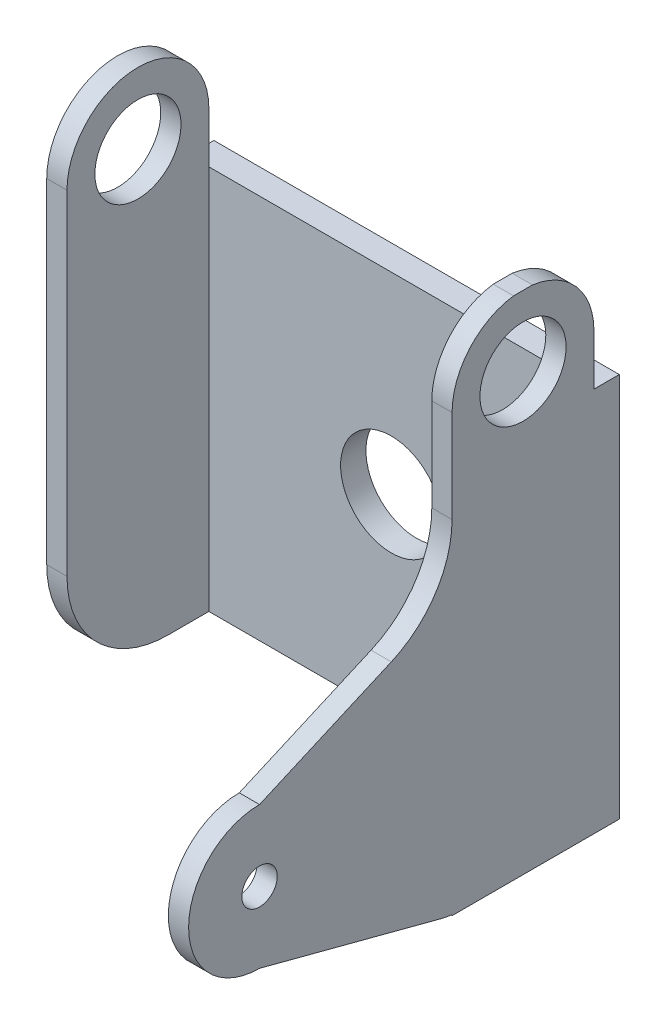
SolidWorks part; units mm, degrees
ref_plane "前视基准面" through (0, 0, 0) normal (0, 0, 1) x (1, 0, 0)
ref_plane "上视基准面" through (0, 0, 0) normal (0, 1, 0) x (1, 0, 0)
ref_plane "右视基准面" through (0, 0, 0) normal (1, 0, 0) x (0, 0, -1)
sketch "草图1" plane through (0, 0, 0) normal (0, 0, 1) x (1, 0, 0)
  line L1 (-20, -19) -> (20, -19)
  line L2 (-20, -19) -> (-20, 19)
  line L3 (-20, 19) -> (20, 19)
  line L4 (20, -19) -> (20, 19)
  line L5 (-20, -19) -> (20, 19) construction
  line L6 (-20, 19) -> (20, -19) construction
  circle A0 centre (0, 0) radius 5
  point P0 (0, 0)
  dimension "D3" = 10
  dimension "D1" = 40
  dimension "D2" = 38
extrude "凸台-拉伸1" add sketch "草图1" along normal blind 2.5
sketch "草图2" plane through (0, 0, 2.5) normal (0, 0, 1) x (1, 0, 0)
  line L0 (-18, 19) -> (-18, -19)
  line L4 (20, -19) -> (20, 19)
  line L5 (20, 19) -> (-20, 19)
  line L6 (-20, 19) -> (-20, -19)
  line L7 (-20, -19) -> (20, -19)
  line L10 (-20, 19) -> (-20, -19)
  line L12 (-18, 19) -> (-18, 31)
  line L13 (-18, 31) -> (-20, 31)
  line L14 (-20, 31) -> (-20, 19)
  line L15 (-20, -19) -> (-18, -19)
  line L16 (0, 28.2188) -> (0, -23.9099) construction
  line L20 (15.5, -19) -> (20, -19)
  line L21 (-20, -19) -> (20, -19) construction
  dimension "D2" = 2
  dimension "D4" = 38
  dimension "D5" = 12
  dimension "D1" = 0
extrude "凸台-拉伸2" add sketch "草图2" along normal blind 14 contours L0 L15 L10 L14 L13 L12
sketch "草图3" plane through (-18, 0, 0) normal (1, 0, 0) x (0, 0, -1)
  line L0 (-16.5, -19) -> (-16.5, 31) construction
  line L1 (-16.5, 31) -> (-2.5, 31) construction
  line L2 (-16.5, -19) -> (-2.5, -19) construction
  line L3 (-2.5, 19) -> (-2.5, -19) construction
  line L4 (-2.5, 31) -> (-2.5, 19) construction
  line L5 (-6.5, -19) -> (-2.5, -19)
  line L6 (-2.5, 19) -> (-2.5, -19)
  line L7 (-16.5, -9) -> (-16.5, 24)
  line L8 (-2.5, 24) -> (-2.5, 19)
  line L9 (-16.5, 24) -> (-16.5, -9)
  line L10 (-2.5, 24) -> (-2.5, -19)
  line L11 (-16.5, -19) -> (-16.5, 31)
  line L12 (-16.5, -19) -> (-2.5, -19)
  line L13 (-16.5, 24) -> (-16.5, 31)
  line L14 (-16.5, 31) -> (-2.5, 31) construction
  line L15 (-16.5, 31) -> (-2.5, 31)
  line L16 (-2.5, 31) -> (-2.5, 24)
  arc A0 (-2.5, 24) -> (-16.5, 24) centre (-9.5, 24) ccw
  arc A1 (-6.5, -19) -> (-16.5, -9) centre (-6.5, -9) cw
  circle A2 centre (-9.5, 24) radius 4.25
  line M1 (-2.5, 19) -> (-2.5, 31)
  line M2 (-2.5, 31) -> (-16.5, 31)
  line M3 (-16.5, 31) -> (-16.5, -19)
  line M4 (-16.5, -19) -> (-2.5, -19)
  dimension "D1" = 14
  dimension "D3" = 7
  dimension "D4" = 10
  dimension "D5" = 8.5
  dimension "D2" = 7
extrude "切除-拉伸2" cut sketch "草图3" against normal through all contours A1 M4 M3 | A0 L15 M3 | A0 M1 M2 | A2
sketch "草图4" plane through (0, 0, 2.5) normal (0, 0, 1) x (1, 0, 0)
  line L1 (20, 19) -> (-18, 19) construction
  line L2 (-18, -19) -> (20, -19) construction
  line L4 (18, -19) -> (18, 30.9375)
  line L5 (15.5, -19) -> (20, -19)
  line L6 (18, 30.9375) -> (20, 30.9375)
  line L7 (20, 30.9375) -> (20, 19)
  line L8 (20, 19) -> (-18, 19)
  line L9 (-18, 19) -> (-18, -19)
  line L10 (-18, -19) -> (20, -19)
  line L11 (20, -19) -> (20, 19)
  line L12 (20, 19) -> (15.5, 19)
  line L14 (15.5, -19) -> (20, -19)
  line L15 (20, -19) -> (20, 19)
  line M7 (20, 19) -> (-18, 19)
  line M9 (-18, -19) -> (20, -19)
  line M10 (20, -19) -> (20, 19)
  dimension "D1" = 2
  dimension "D3" = 50
  dimension "D2" = 0
extrude "凸台-拉伸3" add sketch "草图4" along normal blind 40 contours L7 L6 L4 M7 | L4 M9 M10 M7
sketch "草图5" plane through (20, 0, 0) normal (1, 0, 0) x (0, 0, -1)
  line L0 (-2.5, 25) -> (-2.5, -19)
  line L1 (-16.5, 24) -> (-16.5, 14.8521)
  line L2 (-6.5, -19) -> (-2.5, -19)
  line L3 (-16.5, -18.916) -> (-16.5, -19)
  line L4 (-15.2062, -19) -> (-13.4997, -19)
  line L5 (-35.5, -14) -> (-17.7512, -18.6707)
  line L6 (0, -19) -> (0, 19)
  line L7 (0, 19) -> (-2.5, 19)
  line L8 (-2.5, 19) -> (-2.5, 30.9375)
  line L9 (-2.5, 30.9375) -> (-42.5, 30.9375)
  line L10 (-42.5, 30.9375) -> (-42.5, -19)
  line L11 (-42.5, -19) -> (0, -19)
  line L12 (0, -19) -> (0, 19)
  line L13 (0, 19) -> (-2.5, 19)
  line L14 (-2.5, 19) -> (-2.5, 25)
  line L15 (-9.5, 30.9375) -> (-42.5, 30.9375)
  line L16 (-42.5, 30.9375) -> (-42.5, -19)
  line L17 (-42.5, -19) -> (0, -19)
  line L18 (-35.5, 0) -> (-22.4921, 5.6904)
  line L19 (-9.5, 30.9375) -> (-2.5, 30.9375)
  line L20 (-2.5, 24) -> (-2.5, 30.9375)
  line L21 (-35.5, -7) -> (-9.5, -5.6236) construction
  line L22 (-9.5, -5.6236) -> (-9.5, 24) construction
  arc A0 (-2.5, 24) -> (-16.5, 24) centre (-9.5, 24) ccw
  arc A1 (-15.2062, -19) -> (-17.7512, -18.6707) centre (-15.2062, -9) cw
  arc A2 (-35.5, 0) -> (-35.5, -14) centre (-35.5, -7) ccw
  arc A3 (-16.5, 14.8521) -> (-22.4921, 5.6904) centre (-26.5, 14.8521) cw
  circle A4 centre (-9.5, 24) radius 4.25
  circle A5 centre (-35.5, -7) radius 1.75
  point P14 (-16.5, -19)
  line M9 (-2.5, 19) -> (-2.5, 30.9375)
  line M10 (-2.5, 30.9375) -> (-42.5, 30.9375)
  line M11 (-42.5, 30.9375) -> (-42.5, -19)
  line M12 (-42.5, -19) -> (0, -19)
  dimension "D2" = 14
  dimension "D4" = 10
  dimension "D5" = 14
  dimension "D8" = 10
  dimension "D9" = 8.5
  dimension "D10" = 3.5
  dimension "D3" = 7
  dimension "D6" = 7
  dimension "D7" = 12
  dimension "D11" = 29.6236
  dimension "D1" = 0
extrude "切除-拉伸3" cut sketch "草图5" against normal up to next contours A2 L16 L3 A1 L5 M12 | A3 L1 A0 L15 A2 L18 M11 | A0 L14 M9 M10 | A5 | A4
